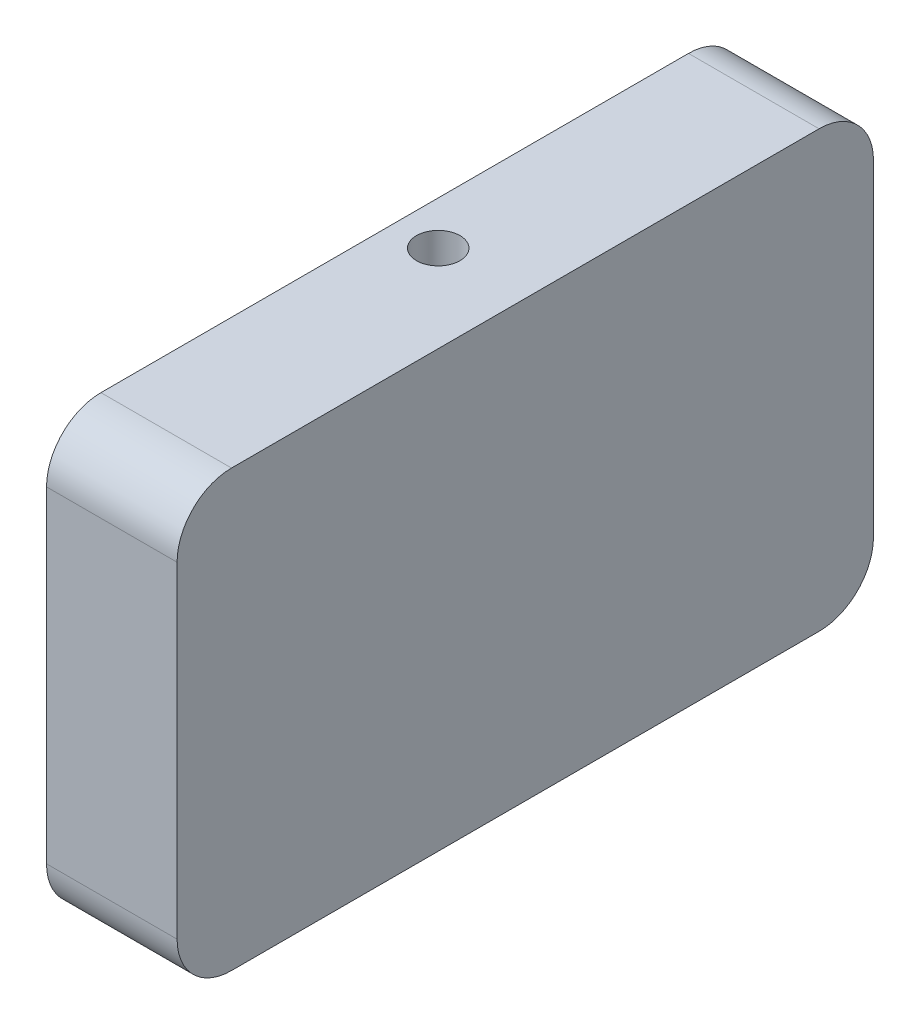
SolidWorks part; units mm, degrees
material "普通碳钢"
ref_plane "前视基准面" through (0, 0, 0) normal (0, 0, 1) x (1, 0, 0)
ref_plane "上视基准面" through (0, 0, 0) normal (0, 1, 0) x (1, 0, 0)
ref_plane "右视基准面" through (0, 0, 0) normal (1, 0, 0) x (0, 0, -1)
sketch "草图1" plane through (0, 0, 0) normal (1, 0, 0) x (0, 0, -1)
  line L1 (-27, 20) -> (27, 20)
  line L2 (-32, 15) -> (-32, -15)
  line L3 (-27, -20) -> (27, -20)
  line L4 (32, 15) -> (32, -15)
  line L5 (-32, 20) -> (32, -20) construction
  line L6 (-32, -20) -> (32, 20) construction
  arc A0 (27, 20) -> (32, 15) centre (27, 15) cw
  arc A1 (27, -20) -> (32, -15) centre (27, -15) ccw
  arc A2 (-27, -20) -> (-32, -15) centre (-27, -15) cw
  arc A3 (-32, 15) -> (-27, 20) centre (-27, 15) cw
  point P0 (0, 0)
  dimension "D3" = 5
  dimension "D1" = 64
  dimension "D2" = 40
extrude "凸台-拉伸1" add sketch "草图1" along normal blind 12
sketch "草图2" plane through (0, 0, 0) normal (-1, 0, 0) x (0, 0, 1)
  circle A1 centre (0, 0) radius 7
  dimension "D1" = 14
extrude "切除-拉伸1" cut sketch "草图2" against normal blind 8 contours A1
sketch "草图4" plane through (12, 0, 0) normal (1, 0, 0) x (0, 0, -1)
  circle A1 centre (0, 0) radius 7
  circle A2 centre (0, 0) radius 7 construction
  dimension "D1" = 0
sketch "草图5" plane through (0, -20, 0) normal (0, -1, 0) x (1, 0, 0)
  line L0 (0, 27) -> (0, -27) construction
  circle A0 centre (4, 0) radius 2
  point P4 (0, 0)
  point P5 (0, 0)
  point P6 (0, 0)
  dimension "D1" = 4
  dimension "D2" = 4
extrude "切除-拉伸2" cut sketch "草图5" against normal through all
